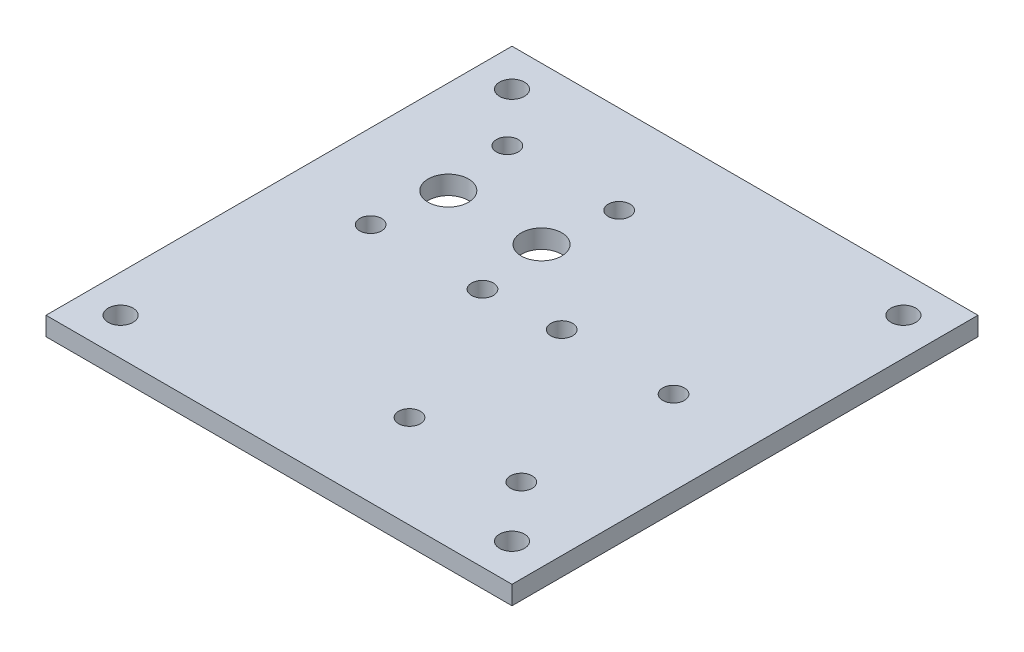
SolidWorks part; units mm, degrees
material "5052-H32"
ref_plane "Front Plane" through (0, 0, 0) normal (0, 0, 1) x (1, 0, 0)
ref_plane "Top Plane" through (0, 0, 0) normal (0, 1, 0) x (1, 0, 0)
ref_plane "Right Plane" through (0, 0, 0) normal (1, 0, 0) x (0, 0, -1)
sketch "Sketch1" plane through (0, 0, 0) normal (0, 1, 0) x (1, 0, 0)
  line L1 (-37.5, -37.5) -> (37.5, -37.5)
  line L2 (-37.5, -37.5) -> (-37.5, 37.5)
  line L3 (-37.5, 37.5) -> (37.5, 37.5)
  line L4 (37.5, -37.5) -> (37.5, 37.5)
  line L5 (-37.5, -37.5) -> (37.5, 37.5) construction
  line L6 (-37.5, 37.5) -> (37.5, -37.5) construction
  line L7 (-30, -2.75) -> (0, -2.75) construction
  line L8 (-30, 9.25) -> (-30, -2.75) construction
  line L9 (0, 9.25) -> (0, -2.75) construction
  line L10 (-30, 27.25) -> (0, 27.25) construction
  line L11 (0, 27.25) -> (0, 15.25) construction
  line L12 (-30, 27.25) -> (-30, 15.25) construction
  circle A0 centre (31.5, 31.5) radius 2
  circle A1 centre (31.5, -31.5) radius 2
  circle A2 centre (-31.5, -31.5) radius 2
  circle A3 centre (-31.5, 31.5) radius 2
  circle A4 centre (-22.5, 12.25) radius 3.25
  circle A5 centre (-7.5, 12.25) radius 3.25
  circle A6 centre (-24, 23.25) radius 1.75
  circle A7 centre (-6, 23.25) radius 1.75
  circle A8 centre (-24, 1.25) radius 1.75
  circle A9 centre (-6, 1.25) radius 1.75
  circle A10 centre (6, -22.5) radius 1.75
  circle A11 centre (24, -22.5) radius 1.75
  circle A12 centre (24, 2) radius 1.75
  circle A13 centre (6, 2) radius 1.75
  point P0 (0, 0)
  point P17 (0, 0)
  dimension "D4" = 4
  dimension "D6" = 3.5
  dimension "D7" = 4
  dimension "D8" = 6
  dimension "D9" = 6
  dimension "D10" = 6.5
  dimension "D11" = 4
  dimension "D12" = 3.5
  dimension "D13" = 4
  dimension "D14" = 4
  dimension "D15" = 6
  dimension "D16" = 6
  dimension "D17" = 15
  dimension "D18" = 15
  dimension "D20" = 15
  dimension "D1" = 75
  dimension "D2" = 75
  dimension "D3" = 6
  dimension "D19" = 15
  dimension "D5" = 4
extrude "Boss-Extrude1" add sketch "Sketch1" along normal blind 3
